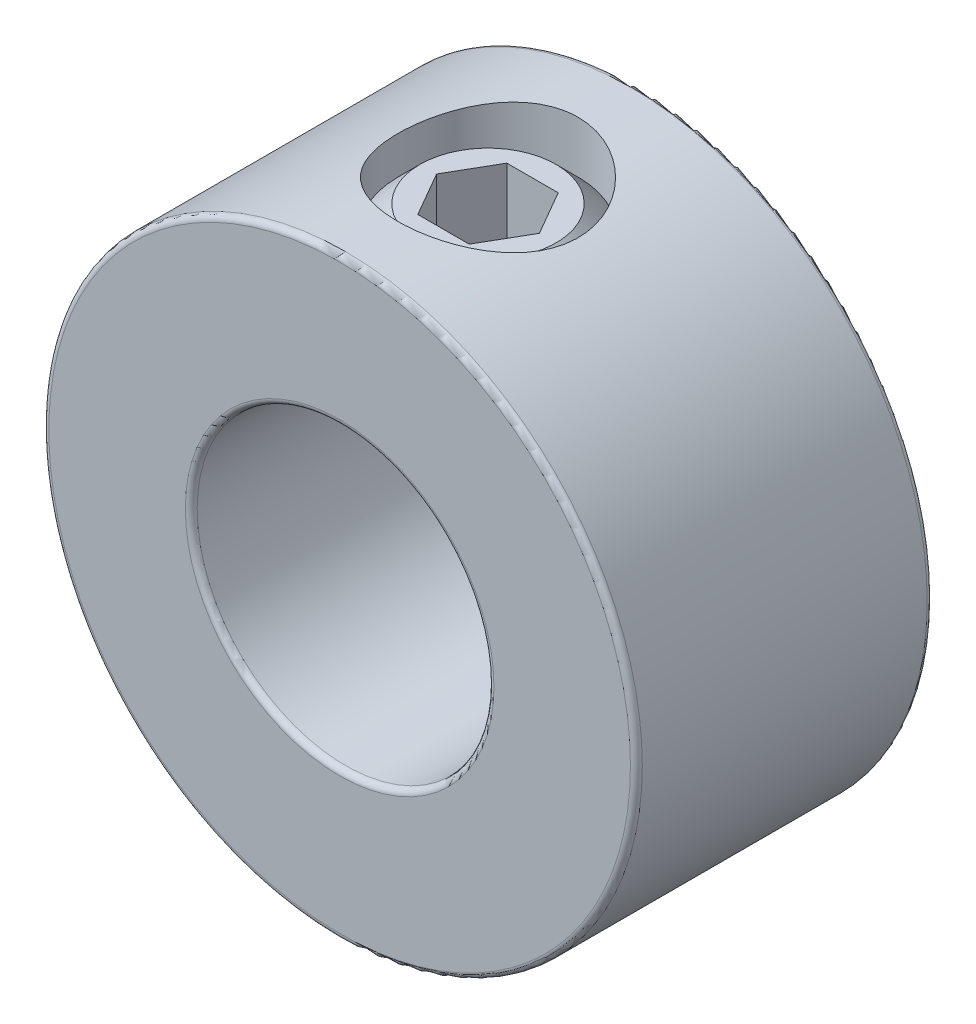
SolidWorks part; units mm, degrees
ref_plane "Front Plane" through (0, 0, 0) normal (0, 0, 1) x (1, 0, 0)
ref_plane "Top Plane" through (0, 0, 0) normal (0, 1, 0) x (1, 0, 0)
ref_plane "Right Plane" through (0, 0, 0) normal (1, 0, 0) x (0, 0, -1)
sketch "Sketch1" plane through (0, 0, 0) normal (0, 0, 1) x (1, 0, 0)
  circle A0 centre (0, 0) radius 7.9375
  circle A1 centre (0, 0) radius 3.9688
  point P4 (7.9375, 0)
  dimension "Bore Dia" = 7.9375
  dimension "OD" = 15.875
extrude "Extrude1" add sketch "Sketch1" along normal mid plane 7.9375
sketch "Sketch2" plane through (41.275, 0, 0) normal (0, -1, 0) x (0, 0, -1)
  line L0 (3.9688, -41.275) -> (-3.9688, -41.275) construction
  line L1 (-3.9688, -33.3375) -> (-3.9688, -49.2125) construction
  line L2 (3.9688, -49.2125) -> (3.9688, -33.3375) construction
  circle A0 centre (0, -41.275) radius 2.413
  point P7 (0, -43.688)
  dimension "Set Screw Dia" = 4.826
extrude "Cut-Extrude1" cut sketch "Sketch2" against normal through all
fillet "Fillet1" radius 0.1588 4 edges at (3.9688, 0, -3.9688) (3.9688, 0, 3.9688) (7.9375, 0, -3.9688) (7.9375, 0, 3.9688)
sketch "Sketch3" plane through (0, 0, 0) normal (0, 0, 1) x (1, 0, 0)
  line L0 (-1.8198, 3.9688) -> (-0.7119, 3.9688)
  line L1 (0, 4.6806) -> (-0.7119, 3.9688)
  line L2 (0, 4.6806) -> (0, 7.1437)
  line L3 (0, 7.1437) -> (-1.8198, 7.1437)
  line L4 (-2.413, 4.562) -> (-2.413, 6.5505)
  line L5 (0, 3.9688) -> (0, 0) construction
  line L6 (-2.413, 4.562) -> (-2.413, 3.9688) construction
  line L7 (-2.413, 3.9688) -> (-1.8198, 3.9688) construction
  line L8 (-2.413, 6.5505) -> (-2.413, 7.1437) construction
  line L9 (-1.8198, 3.9688) -> (-2.413, 4.562)
  line L10 (-2.413, 6.5505) -> (-1.8198, 7.1437)
  line L11 (-2.413, 7.1437) -> (-1.8198, 7.1437) construction
  line L12 (-0.7119, 3.9688) -> (0, 3.9688) construction
  line L13 (0, 3.9688) -> (0, 4.6806) construction
  circle A1 centre (0, 0) radius 3.9688 construction
  dimension "Screw Length" = 3.175
  dimension "D2" = 0.5932
  dimension "D1" = 0.7119
revolve "Revolve1" add sketch "Sketch3" angle 360 about L5
sketch "Sketch4" plane through (3.3734, 7.1437, 0) normal (0, -1, 0) x (0, 0, -1)
  line L1 (0, -1.9986) -> (-1.1906, -2.686)
  line L2 (-1.1906, -2.686) -> (-1.1906, -4.0608)
  line L3 (-1.1906, -4.0608) -> (0, -4.7483)
  line L4 (0, -4.7483) -> (1.1906, -4.0608)
  line L5 (1.1906, -4.0608) -> (1.1906, -2.686)
  line L6 (1.1906, -2.686) -> (0, -1.9986)
  circle A0 centre (0, -3.3734) radius 1.1906 construction
  circle A1 centre (0, -3.3734) radius 1.3748 construction
  dimension "D1" = 2.7496
  dimension "Hex Size" = 2.3813
extrude "Cut-Extrude2" cut sketch "Sketch4" along normal blind 2.3813
equation "\"D1@Fillet1\" = \"OD@Sketch1\"*.01"
equation "\"D1@Cut-Extrude2\" = \"Hex Size@Sketch4\""
equation "\"D2@Sketch3\" =(\"Set Screw Dia@Sketch2\"-\"D1@Sketch4\")/3.5"
equation "\"D1@Sketch3\" = \"D2@Sketch3\"*1.2"
